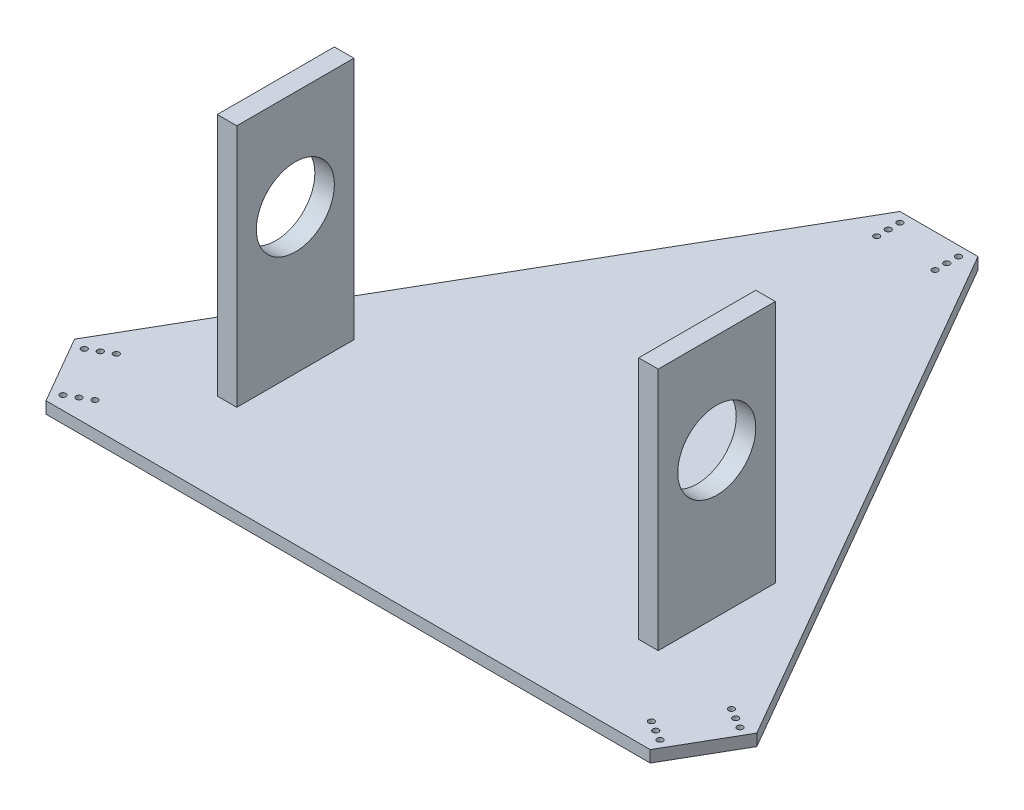
SolidWorks part; units mm, degrees
material "3003 Alloy"
ref_plane "Front Plane" through (0, 0, 0) normal (0, 0, 1) x (1, 0, 0)
ref_plane "Top Plane" through (0, 0, 0) normal (0, 1, 0) x (1, 0, 0)
ref_plane "Right Plane" through (0, 0, 0) normal (1, 0, 0) x (0, 0, -1)
sketch "Sketch8" plane through (0, 0, 0) normal (0, 1, 0) x (1, 0, 0)
  line L0 (-20, 190.359) -> (20, 190.359)
  line L1 (-154.8557, -112.5) -> (154.8557, -112.5)
  line L2 (174.8557, -77.859) -> (20, 190.359)
  line L3 (-20, 190.359) -> (-174.8557, -77.859)
  line L4 (174.8557, -77.859) -> (154.8557, -112.5)
  line L5 (-154.8557, -112.5) -> (-174.8557, -77.859)
  circle A0 centre (0, 0) radius 150 construction
  point P14 (0, 0)
  point P16 (0, 0)
  dimension "D1" = 3
extrude "Boss-Extrude2" add sketch "Sketch8" along normal blind 6 contours L3 L5 L1 L4 L2 L0
sketch "Sketch9" plane through (0, 6, 0) normal (0, 1, 0) x (1, 0, 0)
  line L0 (-20, 190.359) -> (20, 190.359) construction
  circle A0 centre (15, 185.359) radius 1.5
  circle A1 centre (-15, 185.359) radius 1.5
  circle A2 centre (-15, 179.359) radius 1.5
  circle A3 centre (-15, 173.359) radius 1.5
  circle A4 centre (15, 179.359) radius 1.5
  circle A5 centre (15, 173.359) radius 1.5
  circle A6 centre (153.0256, -105.6699) radius 1.5
  circle A7 centre (168.0256, -79.6891) radius 1.5
  circle A8 centre (162.8294, -76.6891) radius 1.5
  circle A9 centre (157.6333, -73.6891) radius 1.5
  circle A10 centre (147.8294, -102.6699) radius 1.5
  circle A11 centre (142.6333, -99.6699) radius 1.5
  circle A12 centre (-168.0256, -79.6891) radius 1.5
  circle A13 centre (-153.0256, -105.6699) radius 1.5
  circle A14 centre (-147.8294, -102.6699) radius 1.5
  circle A15 centre (-142.6333, -99.6699) radius 1.5
  circle A16 centre (-162.8294, -76.6891) radius 1.5
  circle A17 centre (-157.6333, -73.6891) radius 1.5
  point P40 (0, 0)
  dimension "D1" = 5
  dimension "D2" = 2
  dimension "D3" = 3
  dimension "D4" = 3
extrude "Cut-Extrude1" cut sketch "Sketch9" against normal through all
sketch "Sketch10" plane through (0, 6, 0) normal (0, 1, 0) x (1, 0, 0)
  line L0 (0, 190.359) -> (0, -112.5) construction
  line L1 (-20, 190.359) -> (20, 190.359) construction
  line L2 (-154.8557, -112.5) -> (154.8557, -112.5) construction
  line L3 (-113, -6.5477) -> (-113, -66.5477)
  line L4 (103, -6.5477) -> (113, -6.5477)
  line L5 (103, -6.5477) -> (103, -66.5477)
  line L6 (103, -66.5477) -> (113, -66.5477)
  line L7 (113, -6.5477) -> (113, -66.5477)
  line L8 (-103, -6.5477) -> (-103, -66.5477)
  line L9 (-103, -6.5477) -> (-113, -6.5477)
  line L10 (-103, -66.5477) -> (-113, -66.5477)
  dimension "D1" = 10
  dimension "D2" = 60
  dimension "D3" = 226
extrude "Boss-Extrude3" add sketch "Sketch10" along normal blind 125 contours L5 L6 L7 L4 | L3 L10 L8 L9
sketch "Sketch11" plane through (113, 0, 0) normal (1, 0, 0) x (0, 0, -1)
  line L0 (-66.5477, 131) -> (-66.5477, 6) construction
  circle A0 centre (-36.5477, 80) radius 20
  dimension "D1" = 30
extrude "Cut-Extrude2" cut sketch "Sketch11" against normal through all contours A0
